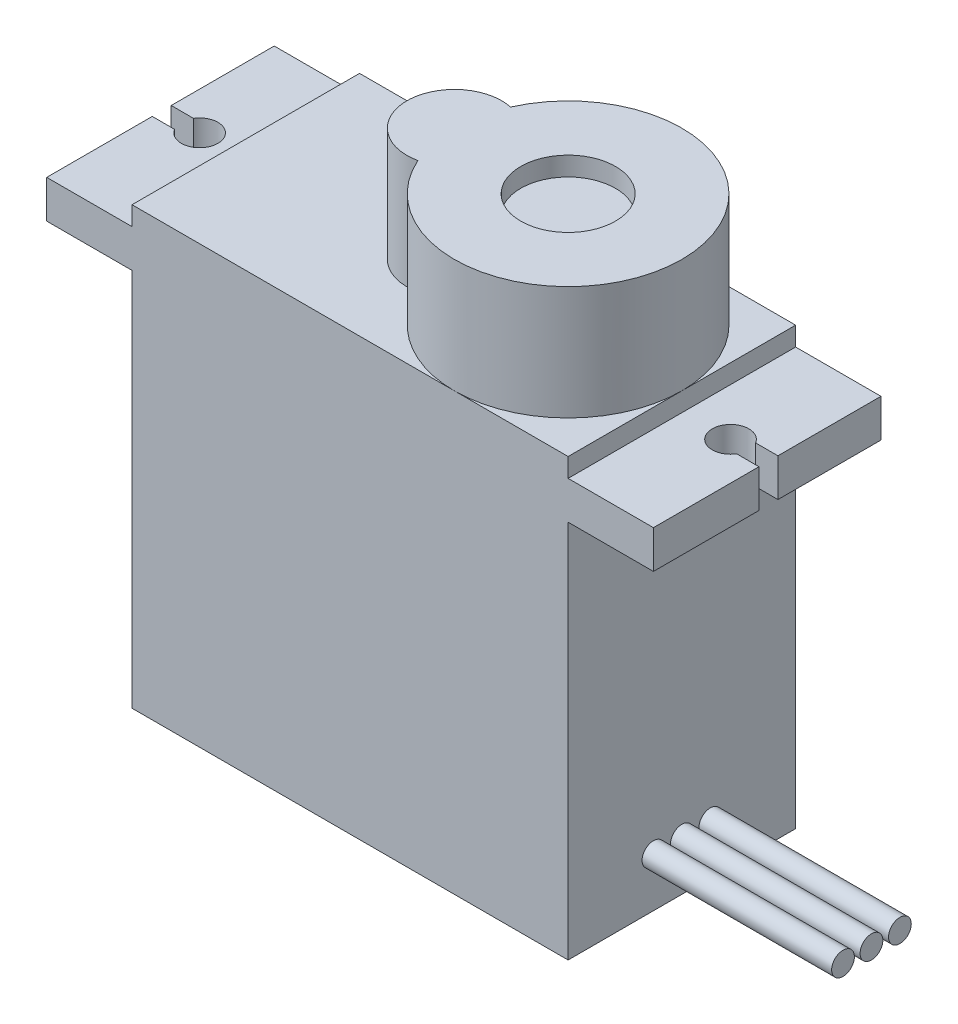
SolidWorks part; units mm, degrees
ref_plane "前视基准面" through (0, 0, 0) normal (0, 0, 1) x (1, 0, 0)
ref_plane "上视基准面" through (0, 0, 0) normal (0, 1, 0) x (1, 0, 0)
ref_plane "右视基准面" through (0, 0, 0) normal (1, 0, 0) x (0, 0, -1)
sketch "草图1" plane through (0, 0, 0) normal (0, 0, 1) x (1, 0, 0)
  line L0 (0, 22.3177) -> (0, -28.6973) construction
  line L1 (-11.5, 11.5) -> (11.5, 11.5)
  line L2 (-11.5, 11.5) -> (-11.5, 10.5)
  line L3 (-11.5, -11.5) -> (11.5, -11.5)
  line L4 (11.5, 11.5) -> (11.5, 10.5)
  line L5 (-11.5, 11.5) -> (11.5, -11.5) construction
  line L6 (-11.5, -11.5) -> (11.5, 11.5) construction
  line L7 (-11.5, 10.5) -> (-16, 10.5)
  line L9 (-11.5, 8.5) -> (-16, 8.5)
  line L10 (-16, 10.5) -> (-16, 8.5)
  line L11 (11.5, 8.5) -> (16, 8.5)
  line L12 (16, 10.5) -> (16, 8.5)
  line L13 (11.5, 10.5) -> (16, 10.5)
  line L15 (11.5, 8.5) -> (11.5, -11.5)
  line L16 (-11.5, 8.5) -> (-11.5, -11.5)
  point P0 (0, 0)
  dimension "D1" = 23
  dimension "D2" = 23
  dimension "D3" = 2
  dimension "D4" = 4.5
  dimension "D5" = 1
extrude "凸台-拉伸1" add sketch "草图1" along normal blind 12
sketch "草图2" plane through (0, 11.5, 0) normal (0, 1, 0) x (1, 0, 0)
  line L0 (11.5, -12) -> (-11.5, -12) construction
  line L1 (11.5, -12) -> (11.5, 0) construction
  arc A0 (0.0208, -8.4451) -> (0.0208, -3.5549) centre (5.5, -6) ccw
  arc A1 (0.0208, -3.5549) -> (0.0208, -8.4451) centre (-0.5, -6) ccw
  dimension "D1" = 5
  dimension "D2" = 12
extrude "凸台-拉伸2" add sketch "草图2" along normal blind 6
sketch "草图3" plane through (0, 17.5, 0) normal (0, 1, 0) x (1, 0, 0)
  circle A0 centre (5.5, -6) radius 2.5
sketch "草图4" plane through (0, 10.5, 0) normal (0, 1, 0) x (1, 0, 0)
  line L0 (11.5, -12) -> (11.5, 0) construction
  line L1 (0, 6.5148) -> (0, -21.0713) construction
  line L2 (16, -5.4334) -> (14.824, -5.4334)
  line L3 (16, -12) -> (16, 0) construction
  line L4 (16, -6.4334) -> (14.824, -6.4334)
  line L5 (16, -6.4334) -> (16, -5.4334)
  line L6 (-16, -5.4334) -> (-14.824, -5.4334)
  line L7 (-16, -6.4334) -> (-16, -5.4334)
  line L8 (-16, -6.4334) -> (-14.824, -6.4334)
  arc A0 (14.824, -5.4334) -> (14.824, -6.4334) centre (14, -5.9334) ccw
  arc A1 (-14.824, -5.4334) -> (-14.824, -6.4334) centre (-14, -5.9334) cw
  point P13 (16, -5.9334)
  dimension "D1" = 2.5
  dimension "D2" = 1
extrude "切除-拉伸1" cut sketch "草图4" against normal blind 5
sketch "草图6" plane through (11.5, 0, 0) normal (1, 0, 0) x (0, 0, -1)
  line L0 (-12, -11.5) -> (0, -11.5) construction
  circle A0 centre (-6, -8.9) radius 0.6
  circle A1 centre (-7.5, -8.9) radius 0.6
  circle A2 centre (-4.5, -8.9) radius 0.6
  point P10 (-6, -11.5)
  dimension "D1" = 1.2
  dimension "D2" = 1.2
  dimension "D3" = 1.2
  dimension "D4" = 1.5
  dimension "D5" = 1.5
  dimension "D6" = 2.6
extrude "凸台-拉伸5" add sketch "草图6" along normal blind 10
extrude "切除-拉伸2" cut sketch "草图3" against normal blind 1
